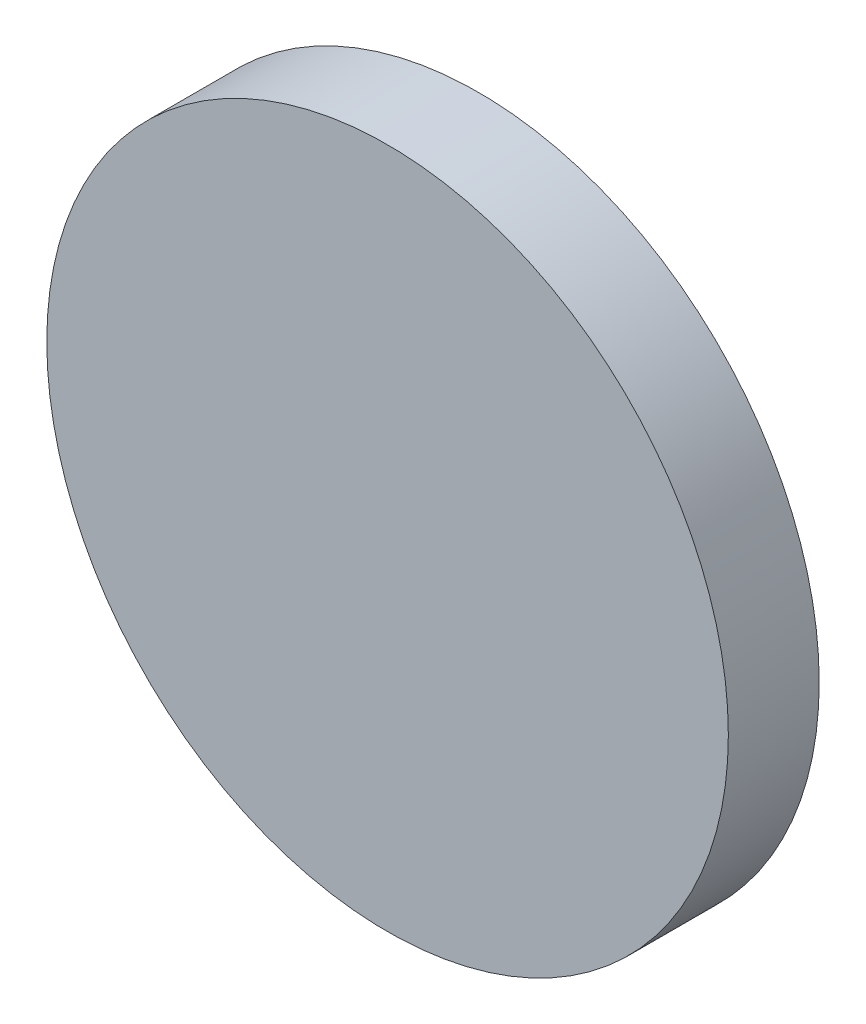
SolidWorks part; units mm, degrees
ref_plane "前视基准面" through (0, 0, 0) normal (0, 0, 1) x (1, 0, 0)
ref_plane "上视基准面" through (0, 0, 0) normal (0, 1, 0) x (1, 0, 0)
ref_plane "右视基准面" through (0, 0, 0) normal (1, 0, 0) x (0, 0, -1)
sketch "草图1" plane through (0, 0, 0) normal (0, 0, 1) x (1, 0, 0)
  circle A0 centre (0, 0) radius 15
  dimension "D1" = 30
extrude "凸台-拉伸1" add sketch "草图1" along normal blind 4 contours A0
